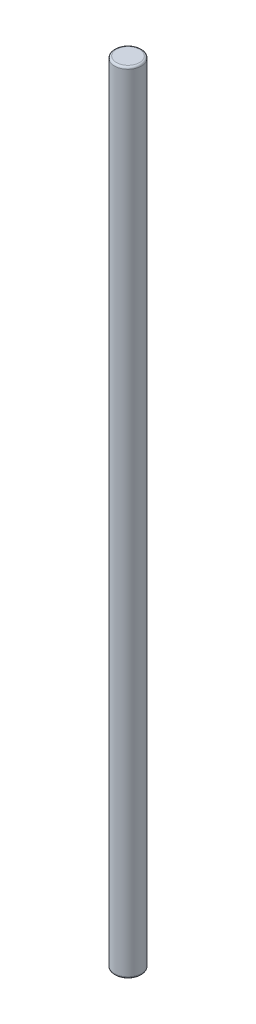
SolidWorks part; units mm, degrees
ref_plane "Front" through (0, 0, 0) normal (0, 0, 1) x (1, 0, 0)
ref_plane "Top" through (0, 0, 0) normal (0, 1, 0) x (1, 0, 0)
ref_plane "Right" through (0, 0, 0) normal (1, 0, 0) x (0, 0, -1)
sketch "Sketch1" plane through (0, 0, 0) normal (0, 1, 0) x (1, 0, 0)
  circle A0 centre (0, 0) radius 0.1715
  dimension "D1" = 0.3429
sketch "Sketch2" plane through (0, 0, 0) normal (0, 0, 1) x (1, 0, 0)
  line L0 (0, 0) -> (0, 6.5826)
  line L1 (0.1715, 0) -> (-0.1715, 0) construction
  line L2 (0.0744, 6.7622) -> (0.4336, 7.1214)
  line L3 (0.508, 7.301) -> (0.508, 8.4185)
  arc A0 (0.4336, 7.1214) -> (0.508, 7.301) centre (0.254, 7.301) ccw
  arc A1 (0, 6.5826) -> (0.0744, 6.7622) centre (0.254, 6.5826) cw
  point P8 (0.508, 7.1958)
  point P11 (0, 6.6878)
  dimension "D5" = 0.254
  dimension "D1" = 0.508
  dimension "D2" = 45
  dimension "D3" = 1.1175
  dimension "D4" = 8.4185
  dimension "D6" = 6.5826
sweep "Sweep1" add profiles "Sketch1" path "Sketch2"
fillet "Fillet1" radius 0.0254 2 edges at (0, 0, 0.1715) (0.508, 8.4185, 0.1715)
sketch "Sketch3" plane through (0, 0, 0) normal (0, 0, 1) x (1, 0, 0)
  line L1 (1.2102, 5.6117) -> (-0.9147, 5.6117)
  line L2 (1.2102, 5.6117) -> (1.2102, 9.4789)
  line L3 (1.2102, 9.4789) -> (-0.9147, 9.4789)
  line L4 (-0.9147, 5.6117) -> (-0.9147, 9.4789)
extrude "Cut-Extrude1" cut sketch "Sketch3" along normal mid plane 2.54
sketch "Sketch4" plane through (0, 5.6117, 0) normal (0, 1, 0) x (1, 0, 0)
  circle A1 centre (0, 0) radius 0.1715
  circle A2 centre (0, 0) radius 0.1715
  dimension "D1" = 0
extrude "Boss-Extrude1" add sketch "Sketch4" along normal offset from surface (4.3959 mm away) 10.0076 up to face at (0, 0, 0.1461)
fillet "Fillet2" radius 0.0254 1 edges at (0, 10.0076, 0.1715)
